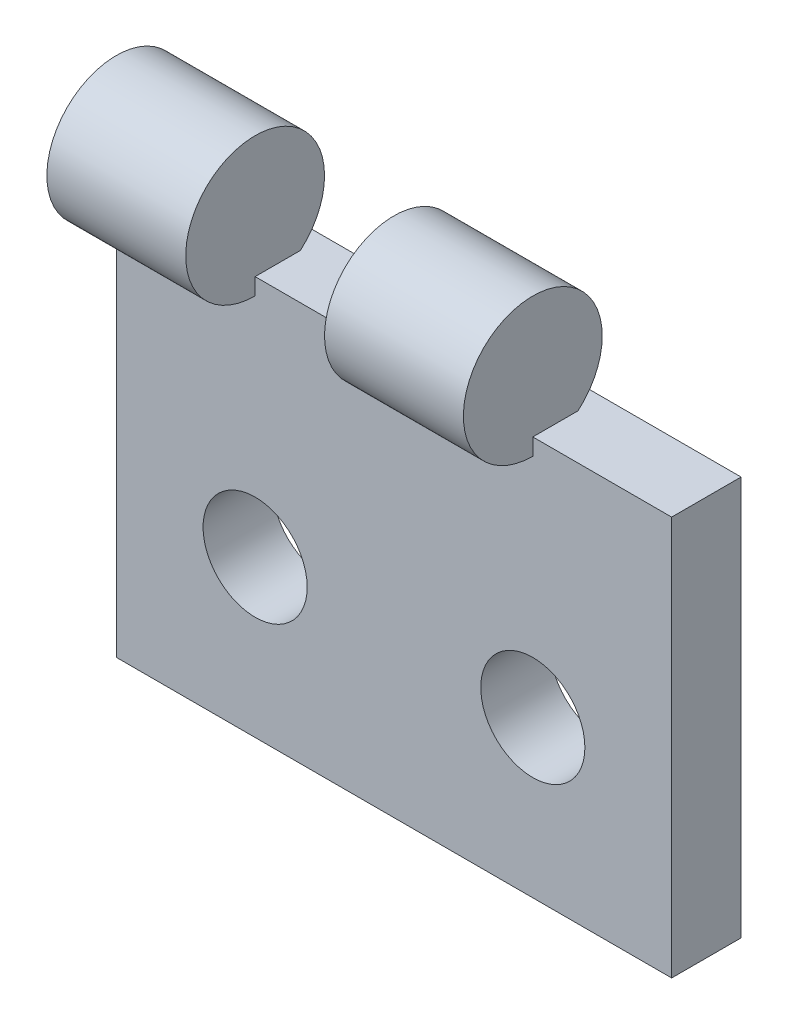
SolidWorks part; units mm, degrees
ref_plane "Front" through (0, 0, 0) normal (0, 0, 1) x (1, 0, 0)
ref_plane "Top" through (0, 0, 0) normal (0, 1, 0) x (1, 0, 0)
ref_plane "Right" through (0, 0, 0) normal (1, 0, 0) x (0, 0, -1)
sketch "Sketch1" plane through (0, 0, 0) normal (0, 0, 1) x (1, 0, 0)
  line L0 (0, 11.5) -> (0, 14.5) construction
  line L1 (0, 0) -> (16, 0)
  line L2 (0, 0) -> (0, 11.5)
  line L3 (0, 11.5) -> (16, 11.5)
  line L4 (16, 0) -> (16, 11.5)
  line L5 (0, 14.5) -> (16, 14.5) construction
  line L6 (16, 14.5) -> (16, 11.5) construction
  dimension "D1" = 16
  dimension "D2" = 14.5
  dimension "D3" = 3
extrude "Boss-Extrude1" add sketch "Sketch1" along normal blind 2
sketch "Sketch2" plane through (0, 0, 0) normal (1, 0, 0) x (0, 0, -1)
  line L0 (0, 11.5) -> (0, 13.0179) construction
  circle A0 centre (-2, 13.0179) radius 2
  point P6 (0, 0)
  dimension "D1" = 4
extrude "Boss-Extrude2" add sketch "Sketch2" along normal blind 4
pattern_linear "LPattern1" count 2 spacing 8 along (1, 0, 0) of "Boss-Extrude2"
hole_wizard "Ø3.0mm Dowel Hole1" positions "Sketch3" profile "Sketch4" hole size "Ø3.0" standard "ANSI Metric" end condition through all
sketch "Sketch3" plane through (0, 0, 2) normal (0, 0, 1) x (1, 0, 0)
  line L0 (0, 11.0179) -> (0, 0) construction
  line L1 (16, 0) -> (16, 11.5) construction
  line L2 (8, 11.5) -> (4, 11.5) construction
  point P0 (4, 4.5)
  point P2 (12, 4.5)
  point P11 (0, 0)
  dimension "D1" = 4
  dimension "D2" = 4
  dimension "D3" = 7
sketch "Sketch4" plane through (4, 4.5, 2) normal (1, 0, 0) x (0, -1, 0)
  line L0 (0, 0) -> (0, 2)
  line L1 (0, 2) -> (1.5, 2)
  line L2 (1.5, 2) -> (1.5, 0)
  line L5 (1.5, 0) -> (0, 0)
  line L11 (0, -6.35) -> (0, 107.95) construction
  dimension "Thru Hole Dia." = 3
  dimension "Thru Hole Depth" = 2
